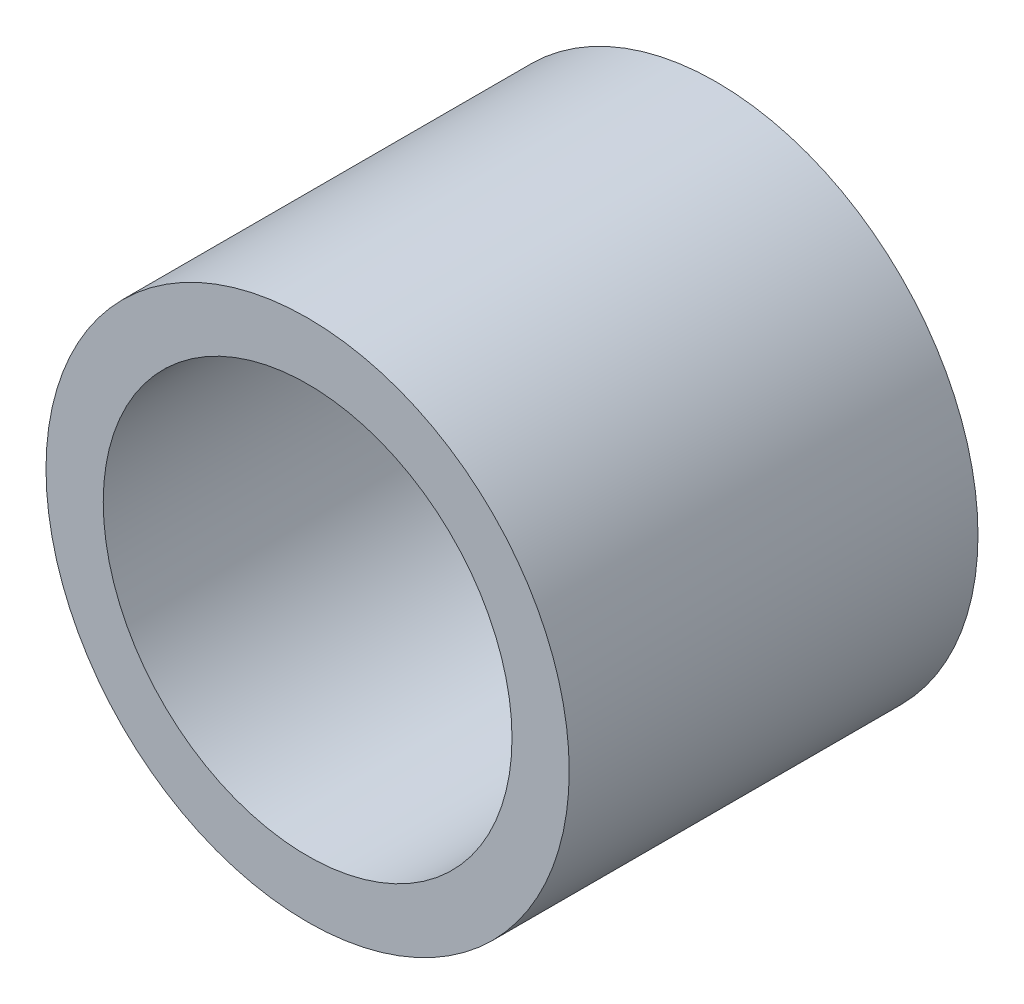
SolidWorks part; units mm, degrees
ref_plane "Front Plane" through (0, 0, 0) normal (0, 0, 1) x (1, 0, 0)
ref_plane "Top Plane" through (0, 0, 0) normal (0, 1, 0) x (1, 0, 0)
ref_plane "Right Plane" through (0, 0, 0) normal (1, 0, 0) x (0, 0, -1)
sketch "Sketch1" plane through (0, 0, 0) normal (0, 0, 1) x (1, 0, 0)
  circle A0 centre (0, 0) radius 16
  circle A1 centre (0, 0) radius 12.5
  dimension "D1" = 25
  dimension "D2" = 32
extrude "Boss-Extrude1" add sketch "Sketch1" along normal mid plane 25
